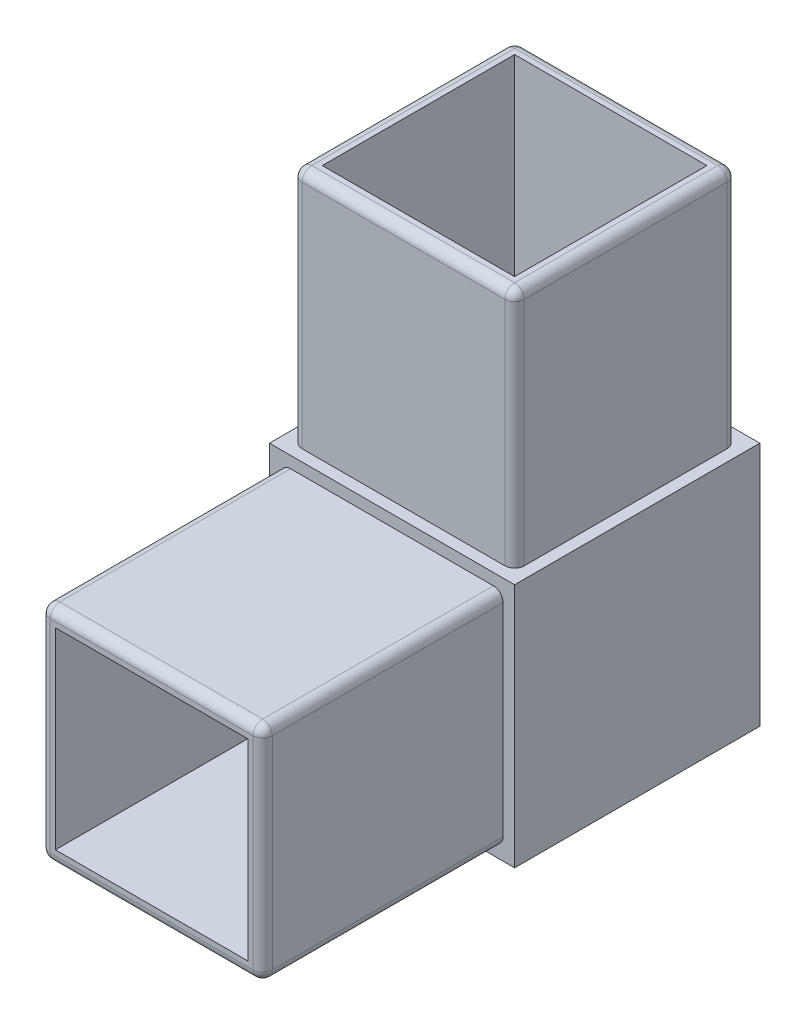
SolidWorks part; units mm, degrees
material "PBT General Purpose"
ref_plane "Front" through (0, 0, 0) normal (0, 0, 1) x (1, 0, 0)
ref_plane "Top" through (0, 0, 0) normal (0, 1, 0) x (1, 0, 0)
ref_plane "Right" through (0, 0, 0) normal (1, 0, 0) x (0, 0, -1)
sketch "Sketch1" plane through (0, 0, 0) normal (0, 1, 0) x (1, 0, 0)
  line L1 (-12.75, 12.75) -> (12.75, 12.75)
  line L2 (-12.75, 12.75) -> (-12.75, -12.75)
  line L3 (-12.75, -12.75) -> (12.75, -12.75)
  line L4 (12.75, 12.75) -> (12.75, -12.75)
  line L5 (-12.75, 12.75) -> (12.75, -12.75) construction
  line L6 (-12.75, -12.75) -> (12.75, 12.75) construction
  point P0 (0, 0)
  dimension "D1" = 25.5
extrude "Boss-Extrude1" add sketch "Sketch1" along normal blind 25.5
sketch "Sketch3" plane through (0, 25.5, 0) normal (0, 1, 0) x (1, 0, 0)
  line L1 (-11.55, 11.55) -> (11.55, 11.55)
  line L2 (-11.55, 11.55) -> (-11.55, -11.55)
  line L3 (-11.55, -11.55) -> (11.55, -11.55)
  line L4 (11.55, 11.55) -> (11.55, -11.55)
  line L5 (-11.55, 11.55) -> (11.55, -11.55) construction
  line L6 (-11.55, -11.55) -> (11.55, 11.55) construction
  point P0 (0, 0)
  dimension "D1" = 23.1
extrude "Boss-Extrude2" add sketch "Sketch3" along normal blind 25
sketch "Sketch5" plane through (0, 0, 12.75) normal (0, 0, 1) x (1, 0, 0)
  line L0 (-11.55, 25.5) -> (11.55, 25.5) construction
  line L1 (-11.55, 24.3) -> (11.55, 24.3)
  line L2 (-11.55, 24.3) -> (-11.55, 1.2)
  line L3 (-11.55, 1.2) -> (11.55, 1.2)
  line L4 (11.55, 24.3) -> (11.55, 1.2)
  line L5 (-11.55, 24.3) -> (11.55, 1.2) construction
  line L6 (-11.55, 1.2) -> (11.55, 24.3) construction
  line L7 (12.75, 25.5) -> (12.75, 0) construction
  point P0 (0, 12.75)
  dimension "D1" = 23.1
  dimension "D2" = 1.2
  dimension "D3" = 1.2
extrude "Boss-Extrude3" add sketch "Sketch5" along normal blind 25
sketch "Sketch6" plane through (0, 0, 37.75) normal (0, 0, 1) x (1, 0, 0)
  line L0 (11.55, 1.2) -> (11.55, 24.3) construction
  line L1 (-10, 22.75) -> (10, 22.75)
  line L2 (-10, 22.75) -> (-10, 2.75)
  line L3 (-10, 2.75) -> (10, 2.75)
  line L4 (10, 22.75) -> (10, 2.75)
  line L5 (-10, 22.75) -> (10, 2.75) construction
  line L6 (-10, 2.75) -> (10, 22.75) construction
  line L7 (-11.55, 1.2) -> (11.55, 1.2) construction
  point P0 (0, 12.75)
  dimension "D1" = 20
  dimension "D2" = 1.55
  dimension "D3" = 1.55
extrude "Cut-Extrude1" cut sketch "Sketch6" against normal blind 45.5
sketch "Sketch7" plane through (0, 50.5, 0) normal (0, 1, 0) x (1, 0, 0)
  line L1 (-10, 10) -> (10, 10)
  line L2 (-10, 10) -> (-10, -10)
  line L3 (-10, -10) -> (10, -10)
  line L4 (10, 10) -> (10, -10)
  line L5 (-10, 10) -> (10, -10) construction
  line L6 (-10, -10) -> (10, 10) construction
  point P0 (0, 0)
  dimension "D1" = 20
extrude "Cut-Extrude2" cut sketch "Sketch7" against normal blind 45.5
fillet "Fillet1" radius 1 16 edges at (0, 1.2, 37.75) (-11.55, 12.75, 37.75) (11.55, 12.75, 37.75) (0, 24.3, 37.75) (-11.55, 50.5, 0) (0, 50.5, -11.55) (11.55, 50.5, 0) (0, 50.5, 11.55) (11.55, 1.2, 25.25) (-11.55, 1.2, 25.25) (-11.55, 24.3, 25.25) (11.55, 24.3, 25.25) (-11.55, 38, 11.55) (-11.55, 38, -11.55) (11.55, 38, -11.55) (11.55, 38, 11.55)
sketch "Sketch9" [suppressed] plane through (0, 1.2, 0) normal (0, -1, 0) x (1, 0, 0)
  line L0 (-10.55, 12.75) -> (10.55, 12.75) construction
  line L1 (-11.55, 12.75) -> (-11.55, 36.75) construction
  circle A0 centre (0, 32.75) radius 4
  dimension "D1" = 8
  dimension "D2" = 20
  dimension "D3" = 11.55
extrude "Cut-Extrude4" [suppressed] cut sketch "Sketch9" against normal through all
